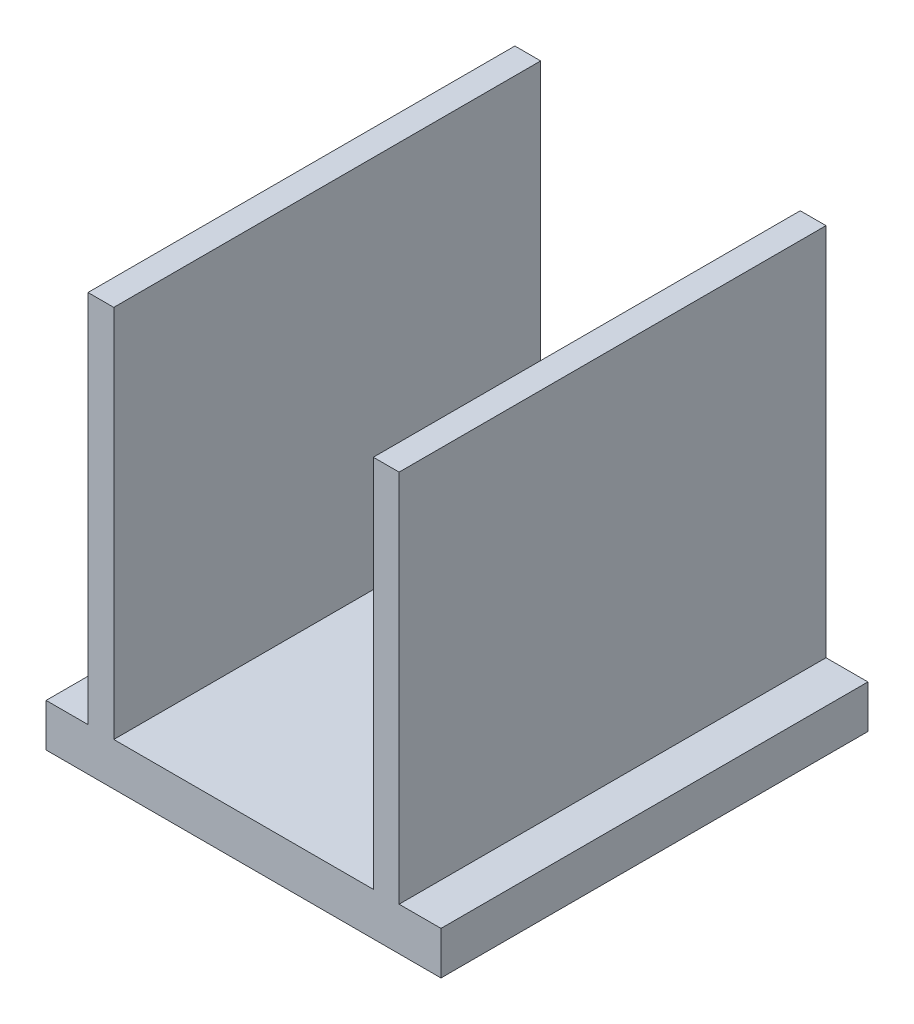
SolidWorks part; units mm, degrees
ref_plane "Front" through (0, 0, 0) normal (0, 0, 1) x (1, 0, 0)
ref_plane "Top" through (0, 0, 0) normal (0, 1, 0) x (1, 0, 0)
ref_plane "Right" through (0, 0, 0) normal (1, 0, 0) x (0, 0, -1)
sketch "Sketch1" plane through (0, 0, 0) normal (0, 1, 0) x (1, 0, 0)
  line L1 (-18.7771, -18.1903) -> (53.593, -18.1903)
  line L2 (-18.7771, -18.1903) -> (-18.7771, 60.0476)
  line L3 (-18.7771, 60.0476) -> (53.593, 60.0476)
  line L4 (53.593, -18.1903) -> (53.593, 60.0476)
extrude "Boss-Extrude1" add sketch "Sketch1" along normal blind 7.874
sketch "Sketch2" plane through (0, 7.874, 0) normal (0, 1, 0) x (1, 0, 0)
  line L0 (17.4079, 60.0476) -> (17.4079, -18.1903) construction
  line L1 (53.593, 60.0476) -> (-18.7771, 60.0476) construction
  line L2 (-18.7771, -18.1903) -> (53.593, -18.1903) construction
  line L3 (-8.7388, 20.9286) -> (43.5547, 20.9286)
  line L4 (45.9173, 60.0476) -> (41.192, 60.0476)
  line L5 (-11.1015, -18.1903) -> (-6.3761, -18.1903)
  line L6 (-11.1015, -18.1903) -> (-11.1015, 60.0476)
  line L7 (-11.1015, 60.0476) -> (-6.3761, 60.0476)
  line L8 (-6.3761, -18.1903) -> (-6.3761, 60.0476)
  line L9 (-11.1015, -18.1903) -> (-6.3761, 60.0476) construction
  line L10 (-11.1015, 60.0476) -> (-6.3761, -18.1903) construction
  line L11 (41.192, -18.1903) -> (41.192, 60.0476)
  line L12 (45.9173, -18.1903) -> (41.192, -18.1903)
  line L13 (45.9173, -18.1903) -> (45.9173, 60.0476)
  line L14 (45.9173, 60.0476) -> (41.192, -18.1903) construction
  line L15 (45.9173, -18.1903) -> (41.192, 60.0476) construction
  point P9 (17.4079, 20.9286)
extrude "Boss-Extrude3" add sketch "Sketch2" along normal blind 68.58
